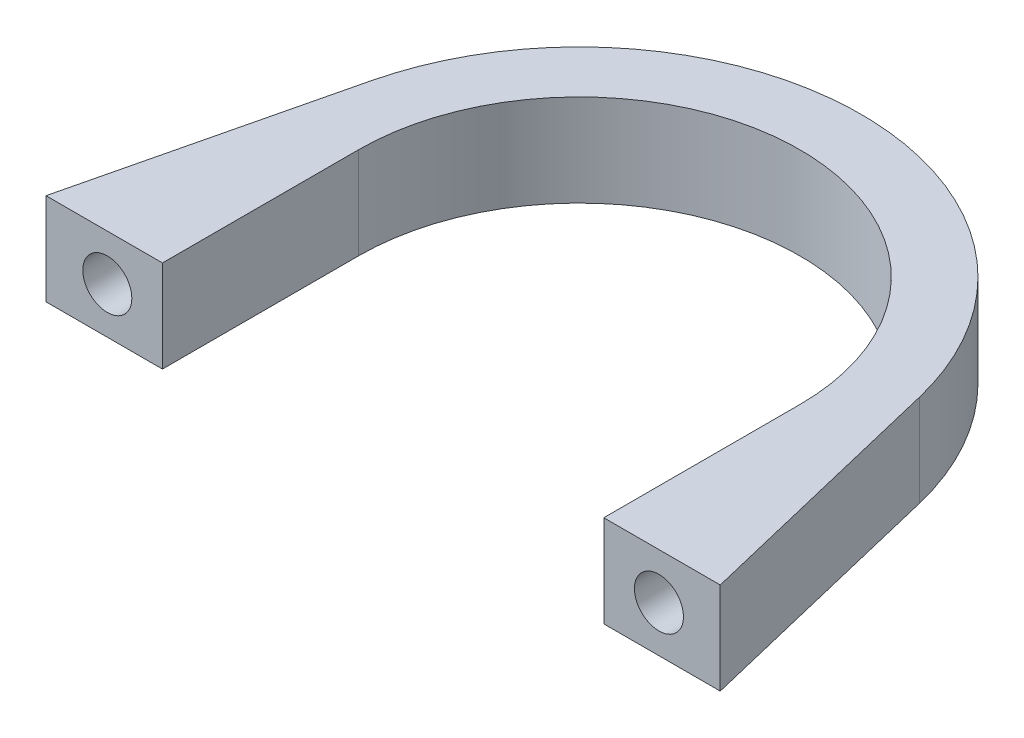
SolidWorks part; units mm, degrees
ref_plane "Ön Düzlem" through (0, 0, 0) normal (0, 0, 1) x (1, 0, 0)
ref_plane "Üst Düzlem" through (0, 0, 0) normal (0, 1, 0) x (1, 0, 0)
ref_plane "Sağ Düzlem" through (0, 0, 0) normal (1, 0, 0) x (0, 0, -1)
sketch "Sketch1" plane through (0, 0, 0) normal (0, 1, 0) x (1, 0, 0)
  line L1 (0, 0) -> (0, -10491.9918) construction
  line L2 (-22.3633, 5.3744) -> (-27.5, -16)
  line L5 (-18, -16) -> (-18, 0)
  line L7 (18, -16) -> (18, 0)
  line L8 (22.3633, 5.3744) -> (27.5, -16)
  line L9 (-27.5, -16) -> (-18, -16)
  line L11 (27.5, -16) -> (18, -16)
  arc A0 (18, 0) -> (-18, 0) centre (0, 0) ccw
  arc A1 (22.3633, 5.3744) -> (-22.3633, 5.3744) centre (0, 0) ccw
  circle A2 centre (0, 0) radius 23 construction
  circle A3 centre (0, 0) radius 18 construction
  point P1 (9, -16.9616)
  dimension "D2" = 36
  dimension "D1" = 16
  dimension "D4" = 55
  dimension "D3" = 5
extrude "Boss-Extrude1" add sketch "Sketch1" along normal blind 7.5
sketch "Sketch2" plane through (0, 0, 16) normal (0, 0, 1) x (1, 0, 0)
  line L0 (-27.5, 7.5) -> (-27.5, 0) construction
  line L1 (-27.5, 7.5) -> (-18, 7.5) construction
  line L2 (-27.5, 7.5) -> (-27.5, 0) construction
  line L3 (-27.5, 7.5) -> (-18, 7.5) construction
  line L4 (0, 0) -> (0, 50000) construction
  line L5 (-18, 0) -> (18, 0) construction
  circle A0 centre (-22.5, 3.75) radius 2
  circle A2 centre (22.5, 3.75) radius 2
  point P7 (-27.5, 3.75)
  point P13 (0, 0)
  point P14 (0, 0)
  dimension "D1" = 4
  dimension "D2" = 45
extrude "Cut-Extrude1" cut sketch "Sketch2" against normal blind 4
